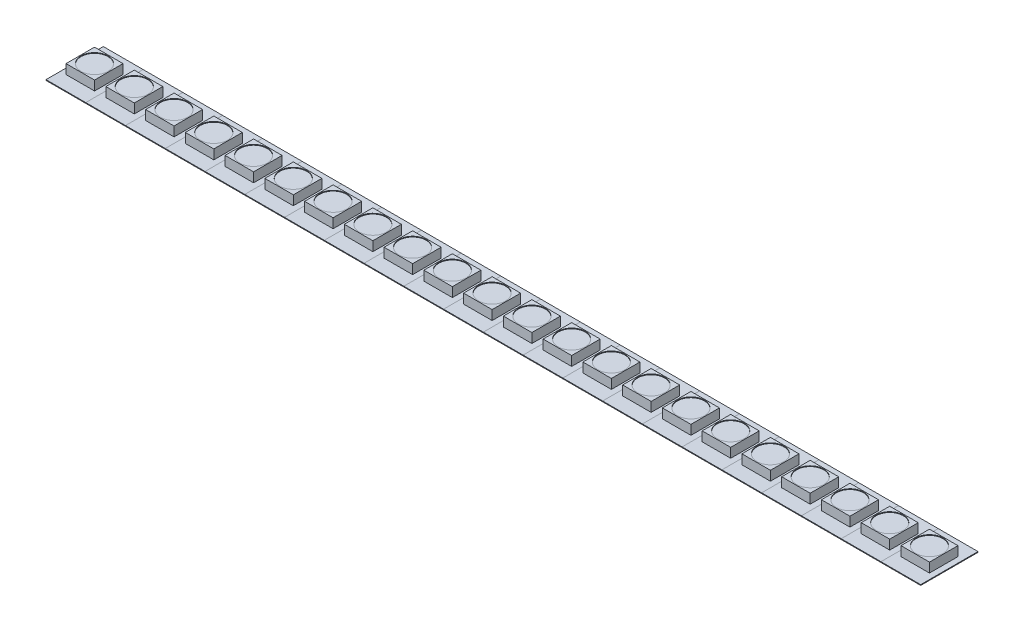
SolidWorks part; units mm, degrees
ref_plane "Front Plane" through (0, 0, 0) normal (0, 0, 1) x (1, 0, 0)
ref_plane "Top Plane" through (0, 0, 0) normal (0, 1, 0) x (1, 0, 0)
ref_plane "Right Plane" through (0, 0, 0) normal (1, 0, 0) x (0, 0, -1)
sketch "Sketch1" plane through (0, 0, 0) normal (0, 1, 0) x (1, 0, 0)
  line L0 (-3.4544, 4.9784) -> (3.4544, -4.9784) construction
  line L1 (-3.4544, 4.9784) -> (3.4544, 4.9784)
  line L2 (-3.4544, 4.9784) -> (-3.4544, -4.9784)
  line L3 (-3.4544, -4.9784) -> (3.4544, -4.9784)
  line L4 (3.4544, 4.9784) -> (3.4544, -4.9784)
  dimension "D1" = 9.9568
  dimension "D2" = 6.9088
extrude "Boss-Extrude1" add sketch "Sketch1" along normal blind 0.127
sketch "Sketch3" plane through (0, 0.127, 0) normal (0, 1, 0) x (1, 0, 0)
  line L0 (-3.4544, 4.9784) -> (3.4544, -4.9784) construction
  line L1 (-2.4765, 2.4765) -> (2.4765, -2.4765) construction
  line L2 (-2.4765, 2.4765) -> (2.4765, 2.4765)
  line L3 (-2.4765, 2.4765) -> (-2.4765, -2.4765)
  line L4 (-2.4765, -2.4765) -> (2.4765, -2.4765)
  line L5 (2.4765, 2.4765) -> (2.4765, -2.4765)
  dimension "D1" = 4.953
extrude "Boss-Extrude3" add sketch "Sketch3" along normal blind 1.651
sketch "Sketch5" plane through (0, 1.778, 0) normal (0, 1, 0) x (1, 0, 0)
  circle A0 centre (0, 0) radius 2.3483
extrude "Cut-Extrude1" cut sketch "Sketch5" against normal blind 0.127
pattern_linear "LPattern1" count 22 spacing 6.9088 along (1, 0, 0) of "Boss-Extrude3", "Cut-Extrude1", "Boss-Extrude1"
